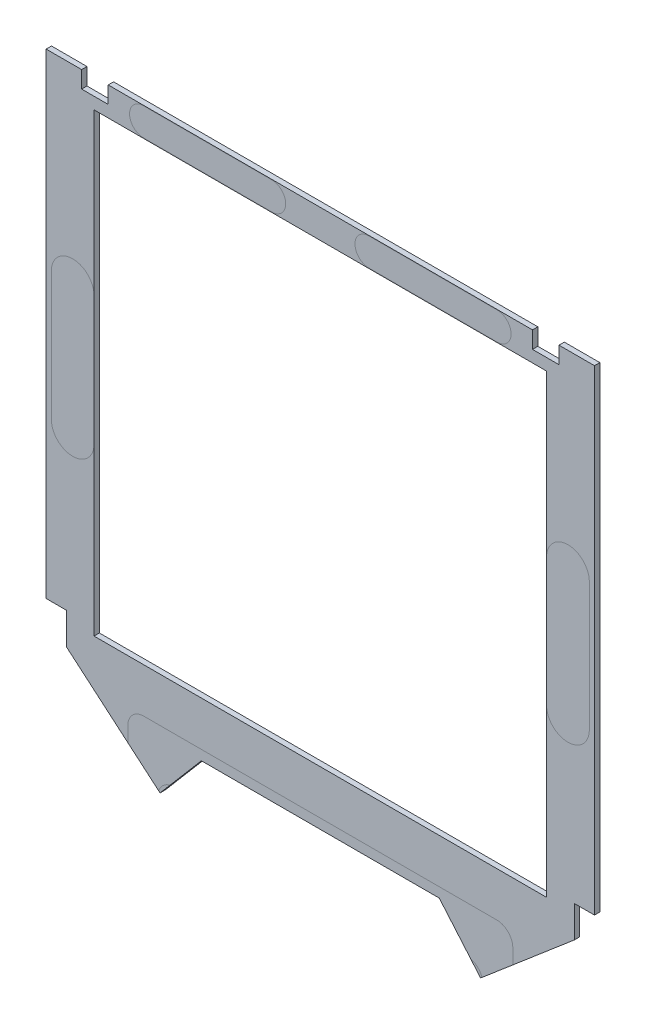
SolidWorks part; units mm, degrees
ref_plane "Front" through (0, 0, 0) normal (0, 0, 1) x (1, 0, 0)
ref_plane "Top" through (0, 0, 0) normal (0, 1, 0) x (1, 0, 0)
ref_plane "Right" through (0, 0, 0) normal (1, 0, 0) x (0, 0, -1)
sketch "Sketch1" plane through (0, 0, -8.9364) normal (0, 0, 1) x (1, 0, 0)
  line L0 (-62.992, 192.0875) -> (62.992, 192.0875)
  line L1 (-66.675, 183.0705) -> (66.675, 183.0705) construction
  line L2 (-66.675, 48.768) -> (66.675, 48.768) construction
  line L3 (-66.675, 48.768) -> (66.675, 48.768) construction
  line L4 (66.675, 183.0705) -> (66.675, 48.768) construction
  line L5 (62.992, 192.0875) -> (62.992, 187.071)
  line L6 (62.992, 187.071) -> (70.866, 187.071)
  line L7 (70.866, 187.071) -> (70.866, 192.0875)
  line L8 (70.866, 192.0875) -> (81.407, 192.0875)
  line L9 (81.407, 192.0875) -> (81.407, 50.8)
  line L10 (81.407, 50.8) -> (75.438, 50.8)
  line L11 (75.438, 50.8) -> (75.438, 41.4295)
  line L12 (75.438, 41.4295) -> (47.5845, 17.7206)
  line L13 (47.5845, 17.7206) -> (35.3184, 32.131)
  line L14 (35.3184, 32.131) -> (-35.3184, 32.131)
  line L15 (-67.183, 183.5785) -> (67.183, 183.5785)
  line L16 (67.183, 183.5785) -> (67.183, 48.26)
  line L17 (-67.183, 48.26) -> (67.183, 48.26)
  line L18 (-67.183, 48.26) -> (67.183, 48.26) construction
  line L19 (81.915, 162.3536) -> (81.915, 172.6784) construction
  line L20 (0, 194.183) -> (0, 11.7602) construction
  line L22 (46.5936, 16.2101) -> (78.9144, 43.7216) construction
  line L23 (-67.183, 183.5785) -> (67.183, 183.5785) construction
  line L24 (-66.675, 183.0705) -> (66.675, 183.0705) construction
  line L25 (-66.675, 183.0705) -> (-66.675, 48.768) construction
  line L26 (-67.183, 183.5785) -> (-67.183, 48.26) construction
  line L27 (33.1388, 192.5955) -> (24.7732, 192.5955) construction
  line L28 (81.915, 192.5955) -> (69.6786, 192.5955) construction
  line L29 (-43.2308, 13.3477) -> (43.2308, 13.3477) construction
  line L34 (-66.675, 183.0705) -> (-66.675, 48.768) construction
  line L35 (-67.183, 183.5785) -> (-67.183, 48.26)
  line L36 (-47.5845, 17.7206) -> (-35.3184, 32.131)
  line L37 (-75.438, 41.4295) -> (-47.5845, 17.7206)
  line L38 (-75.438, 50.8) -> (-75.438, 41.4295)
  line L39 (-81.407, 50.8) -> (-75.438, 50.8)
  line L40 (-81.407, 192.0875) -> (-81.407, 50.8)
  line L41 (-70.866, 192.0875) -> (-81.407, 192.0875)
  line L42 (-70.866, 187.071) -> (-70.866, 192.0875)
  line L43 (-62.992, 187.071) -> (-70.866, 187.071)
  line L44 (-62.992, 192.0875) -> (-62.992, 187.071)
  circle A0 centre (79.375, 46.863) radius 3.937 construction
  circle A3 centre (43.434, 16.5227) radius 3.937 construction
  circle A5 centre (66.929, 191.008) radius 3.937 construction
  circle A7 centre (-66.929, 191.008) radius 3.937 construction
  circle A8 centre (-43.434, 16.5227) radius 3.937 construction
  circle A9 centre (-79.375, 46.863) radius 3.937 construction
  point P29 (0, 183.5785)
  point P30 (0, 183.0705)
  point P66 (0, 48.768)
  point P67 (0, 48.26)
  point P69 (0, 32.131)
  point P78 (0, 192.0875)
  dimension "D6" = 18.7833
  dimension "D1" = 0.508
  dimension "D2" = 0.508
  dimension "D3" = 0.508
  dimension "D4" = 0.508
  dimension "D5" = 0.508
extrude "Boss-Extrude1" add sketch "Sketch1" along normal blind 1.5875
sketch "Sketch2" plane through (0, 0, -7.3489) normal (0, 0, 1) x (1, 0, 0)
  line L2 (67.1735, 135.763) -> (67.1735, 97.663)
  line L3 (79.8735, 97.663) -> (79.8735, 135.763)
  line L4 (67.1735, 135.763) -> (67.1735, 97.663)
  line L5 (79.8735, 97.663) -> (79.8735, 135.763)
  line L6 (-67.1735, 97.663) -> (-67.1735, 135.763)
  line L7 (-79.8735, 135.763) -> (-79.8735, 97.663)
  line L8 (-67.1735, 97.663) -> (-67.1735, 135.763)
  line L9 (-79.8735, 135.763) -> (-79.8735, 97.663)
  line L14 (-57.15, 23.111) -> (-48.4599, 15.7139)
  line L15 (-57.15, 30.2895) -> (-57.15, 23.111)
  line L16 (52.3875, 35.052) -> (-52.3875, 35.052)
  line L17 (57.15, 23.111) -> (57.15, 30.2895)
  line L18 (48.4599, 15.7139) -> (57.15, 23.111)
  line L19 (-33.8657, 12.3825) -> (33.8657, 12.3825)
  line L20 (-57.15, 23.111) -> (-48.4599, 15.7139)
  line L21 (-57.15, 30.2895) -> (-57.15, 23.111)
  line L22 (52.3875, 35.052) -> (-52.3875, 35.052)
  line L23 (57.15, 23.111) -> (57.15, 30.2895)
  line L24 (48.4599, 15.7139) -> (57.15, 23.111)
  line L25 (-33.8657, 12.3825) -> (33.8657, 12.3825)
  line L52 (14.4145, 183.7055) -> (52.5145, 183.7055)
  line L53 (52.5145, 191.9605) -> (14.4145, 191.9605)
  line L54 (14.4145, 183.7055) -> (52.5145, 183.7055)
  line L55 (52.5145, 191.9605) -> (14.4145, 191.9605)
  line L56 (-14.4145, 191.9605) -> (-52.5145, 191.9605)
  line L57 (-52.5145, 183.7055) -> (-14.4145, 183.7055)
  line L58 (-14.4145, 191.9605) -> (-52.5145, 191.9605)
  line L59 (-52.5145, 183.7055) -> (-14.4145, 183.7055)
  arc A4 (73.5235, 91.313) -> (79.8735, 97.663) centre (73.5235, 97.663) ccw
  arc A5 (67.1735, 97.663) -> (73.5235, 91.313) centre (73.5235, 97.663) ccw
  arc A6 (73.5235, 142.113) -> (67.1735, 135.763) centre (73.5235, 135.763) ccw
  arc A7 (79.8735, 135.763) -> (73.5235, 142.113) centre (73.5235, 135.763) ccw
  arc A8 (73.5235, 91.313) -> (79.8735, 97.663) centre (73.5235, 97.663) ccw
  arc A9 (67.1735, 97.663) -> (73.5235, 91.313) centre (73.5235, 97.663) ccw
  arc A10 (73.5235, 142.113) -> (67.1735, 135.763) centre (73.5235, 135.763) ccw
  arc A11 (79.8735, 135.763) -> (73.5235, 142.113) centre (73.5235, 135.763) ccw
  arc A12 (-73.5235, 91.313) -> (-67.1735, 97.663) centre (-73.5235, 97.663) ccw
  arc A13 (-79.8735, 97.663) -> (-73.5235, 91.313) centre (-73.5235, 97.663) ccw
  arc A14 (-73.5235, 142.113) -> (-79.8735, 135.763) centre (-73.5235, 135.763) ccw
  arc A15 (-67.1735, 135.763) -> (-73.5235, 142.113) centre (-73.5235, 135.763) ccw
  arc A16 (-73.5235, 91.313) -> (-67.1735, 97.663) centre (-73.5235, 97.663) ccw
  arc A17 (-79.8735, 97.663) -> (-73.5235, 91.313) centre (-73.5235, 97.663) ccw
  arc A18 (-73.5235, 142.113) -> (-79.8735, 135.763) centre (-73.5235, 135.763) ccw
  arc A19 (-67.1735, 135.763) -> (-73.5235, 142.113) centre (-73.5235, 135.763) ccw
  arc A24 (-52.3875, 35.052) -> (-57.15, 30.2895) centre (-52.3875, 30.2895) ccw
  arc A25 (57.15, 30.2895) -> (52.3875, 35.052) centre (52.3875, 30.2895) ccw
  arc A26 (48.2498, 16.8359) -> (48.4599, 15.7139) centre (53.0023, 17.145) ccw
  arc A27 (48.2498, 16.8359) -> (38.6182, 16.8359) centre (43.434, 16.5227) ccw
  arc A28 (33.8657, 12.3825) -> (38.6182, 16.8359) centre (33.8657, 17.145) ccw
  arc A29 (-38.6182, 16.8359) -> (-33.8657, 12.3825) centre (-33.8657, 17.145) ccw
  arc A30 (-38.6182, 16.8359) -> (-48.2498, 16.8359) centre (-43.434, 16.5227) ccw
  arc A31 (-48.4599, 15.7139) -> (-48.2498, 16.8359) centre (-53.0023, 17.145) ccw
  arc A32 (-52.3875, 35.052) -> (-57.15, 30.2895) centre (-52.3875, 30.2895) ccw
  arc A33 (57.15, 30.2895) -> (52.3875, 35.052) centre (52.3875, 30.2895) ccw
  arc A34 (48.2498, 16.8359) -> (48.4599, 15.7139) centre (53.0023, 17.145) ccw
  arc A35 (48.2498, 16.8359) -> (38.6182, 16.8359) centre (43.434, 16.5227) ccw
  arc A36 (33.8657, 12.3825) -> (38.6182, 16.8359) centre (33.8657, 17.145) ccw
  arc A37 (-38.6182, 16.8359) -> (-33.8657, 12.3825) centre (-33.8657, 17.145) ccw
  arc A38 (-38.6182, 16.8359) -> (-48.2498, 16.8359) centre (-43.434, 16.5227) ccw
  arc A39 (-48.4599, 15.7139) -> (-48.2498, 16.8359) centre (-53.0023, 17.145) ccw
  arc A82 (14.4145, 191.9605) -> (14.4145, 183.7055) centre (14.4145, 187.833) ccw
  arc A83 (52.5145, 183.7055) -> (52.5145, 191.9605) centre (52.5145, 187.833) ccw
  arc A84 (14.4145, 191.9605) -> (14.4145, 183.7055) centre (14.4145, 187.833) ccw
  arc A85 (52.5145, 183.7055) -> (52.5145, 191.9605) centre (52.5145, 187.833) ccw
  arc A86 (-14.4145, 183.7055) -> (-14.4145, 191.9605) centre (-14.4145, 187.833) ccw
  arc A87 (-52.5145, 191.9605) -> (-52.5145, 183.7055) centre (-52.5145, 187.833) ccw
  arc A88 (-14.4145, 183.7055) -> (-14.4145, 191.9605) centre (-14.4145, 187.833) ccw
  arc A89 (-52.5145, 191.9605) -> (-52.5145, 183.7055) centre (-52.5145, 187.833) ccw
  dimension "D1" = 0
  dimension "D2" = 0
  dimension "D3" = 0
  dimension "D4" = 0
  dimension "D5" = 0
split line "Split Line1"
